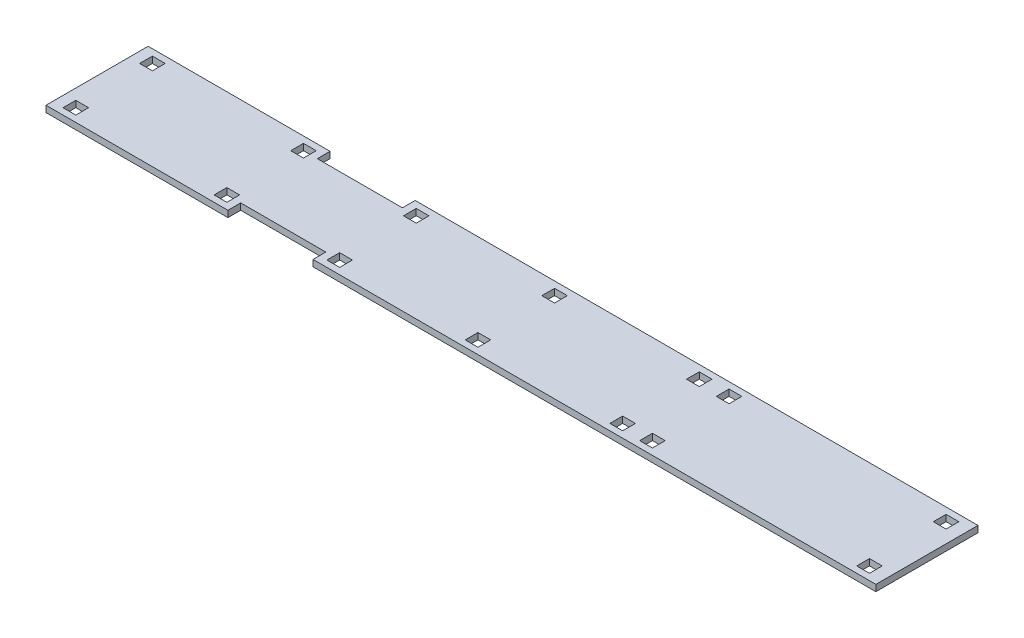
SolidWorks part; units mm, degrees
ref_plane "Front Plane" through (0, 0, 0) normal (0, 0, 1) x (1, 0, 0)
ref_plane "Top Plane" through (0, 0, 0) normal (0, 1, 0) x (1, 0, 0)
ref_plane "Right Plane" through (0, 0, 0) normal (1, 0, 0) x (0, 0, -1)
sketch "Sketch1" plane through (0, 0, 0) normal (0, 1, 0) x (1, 0, 0)
  line L0 (64.5, 4.5) -> (67.5, 4.5)
  line L1 (0, 0) -> (195, 0)
  line L2 (0, 0) -> (0, 24)
  line L3 (0, 24) -> (195, 24)
  line L4 (195, 0) -> (195, 24)
  line L5 (2.5, 22.5) -> (5.5, 22.5)
  line L6 (2.5, 22.5) -> (2.5, 19.5)
  line L7 (2.5, 19.5) -> (5.5, 19.5)
  line L8 (5.5, 22.5) -> (5.5, 19.5)
  line L9 (2.5, 22.5) -> (5.5, 19.5) construction
  line L10 (2.5, 19.5) -> (5.5, 22.5) construction
  line L11 (64.5, 4.5) -> (64.5, 1.5)
  line L12 (64.5, 1.5) -> (67.5, 1.5)
  line L13 (67.5, 4.5) -> (67.5, 1.5)
  line L14 (64.5, 4.5) -> (67.5, 1.5) construction
  line L15 (64.5, 1.5) -> (67.5, 4.5) construction
  line L16 (38, 4.5) -> (41, 4.5)
  line L17 (97, 4.5) -> (100, 4.5)
  line L18 (97, 4.5) -> (97, 1.5)
  line L19 (97, 1.5) -> (100, 1.5)
  line L20 (100, 4.5) -> (100, 1.5)
  line L21 (97, 4.5) -> (100, 1.5) construction
  line L22 (97, 1.5) -> (100, 4.5) construction
  line L23 (38, 4.5) -> (38, 1.5)
  line L24 (38, 1.5) -> (41, 1.5)
  line L25 (41, 4.5) -> (41, 1.5)
  line L26 (38, 4.5) -> (41, 1.5) construction
  line L27 (38, 1.5) -> (41, 4.5) construction
  line L28 (138, 4.5) -> (141, 4.5)
  line L29 (138, 22.5) -> (141, 22.5)
  line L30 (138, 22.5) -> (138, 19.5)
  line L31 (138, 19.5) -> (141, 19.5)
  line L32 (141, 22.5) -> (141, 19.5)
  line L33 (138, 22.5) -> (141, 19.5) construction
  line L34 (138, 19.5) -> (141, 22.5) construction
  line L35 (138, 4.5) -> (138, 1.5)
  line L36 (138, 1.5) -> (141, 1.5)
  line L37 (141, 4.5) -> (141, 1.5)
  line L38 (138, 4.5) -> (141, 1.5) construction
  line L39 (138, 1.5) -> (141, 4.5) construction
  line L40 (131, 4.5) -> (134, 4.5)
  line L41 (131, 22.5) -> (134, 22.5)
  line L42 (131, 22.5) -> (131, 19.5)
  line L43 (131, 19.5) -> (134, 19.5)
  line L44 (134, 22.5) -> (134, 19.5)
  line L45 (131, 22.5) -> (134, 19.5) construction
  line L46 (131, 19.5) -> (134, 22.5) construction
  line L47 (131, 4.5) -> (131, 1.5)
  line L48 (131, 1.5) -> (134, 1.5)
  line L49 (134, 4.5) -> (134, 1.5)
  line L50 (131, 4.5) -> (134, 1.5) construction
  line L51 (131, 1.5) -> (134, 4.5) construction
  line L52 (64.5, 22.5) -> (67.5, 22.5)
  line L53 (97, 22.5) -> (100, 22.5)
  line L54 (97, 22.5) -> (97, 19.5)
  line L55 (97, 19.5) -> (100, 19.5)
  line L56 (100, 22.5) -> (100, 19.5)
  line L57 (97, 22.5) -> (100, 19.5) construction
  line L58 (97, 19.5) -> (100, 22.5) construction
  line L59 (64.5, 22.5) -> (64.5, 19.5)
  line L60 (64.5, 19.5) -> (67.5, 19.5)
  line L61 (67.5, 22.5) -> (67.5, 19.5)
  line L62 (64.5, 22.5) -> (67.5, 19.5) construction
  line L63 (64.5, 19.5) -> (67.5, 22.5) construction
  line L64 (38, 22.5) -> (41, 22.5)
  line L65 (2.5, 4.5) -> (5.5, 4.5)
  line L66 (2.5, 4.5) -> (2.5, 1.5)
  line L67 (2.5, 1.5) -> (5.5, 1.5)
  line L68 (5.5, 4.5) -> (5.5, 1.5)
  line L69 (2.5, 4.5) -> (5.5, 1.5) construction
  line L70 (2.5, 1.5) -> (5.5, 4.5) construction
  line L71 (38, 22.5) -> (38, 19.5)
  line L72 (38, 19.5) -> (41, 19.5)
  line L73 (41, 22.5) -> (41, 19.5)
  line L74 (38, 22.5) -> (41, 19.5) construction
  line L75 (38, 19.5) -> (41, 22.5) construction
  line L76 (189, 22.5) -> (192, 22.5)
  line L77 (189, 4.5) -> (192, 4.5)
  line L78 (189, 4.5) -> (189, 1.5)
  line L79 (189, 1.5) -> (192, 1.5)
  line L80 (192, 4.5) -> (192, 1.5)
  line L81 (189, 4.5) -> (192, 1.5) construction
  line L82 (189, 1.5) -> (192, 4.5) construction
  line L83 (189, 22.5) -> (189, 19.5)
  line L84 (189, 19.5) -> (192, 19.5)
  line L85 (192, 22.5) -> (192, 19.5)
  line L86 (189, 22.5) -> (192, 19.5) construction
  line L87 (189, 19.5) -> (192, 22.5) construction
  point P10 (4, 21)
  point P14 (66, 3)
  point P15 (13.8504, 11.5574)
  point P16 (0, 0)
  point P22 (98.5, 3)
  point P26 (39.5, 3)
  point P32 (139.5, 21)
  point P36 (139.5, 3)
  point P42 (132.5, 21)
  point P46 (132.5, 3)
  point P47 (25.6536, 17.9962)
  point P53 (98.5, 21)
  point P57 (66, 21)
  point P63 (4, 3)
  point P67 (39.5, 21)
  point P73 (190.5, 3)
  point P77 (190.5, 21)
  point P78 (47.2013, 9.4586)
  point P79 (50.0678, 15.2563)
  point P80 (0, 0)
  point P81 (0, 0)
  point P82 (32.4668, 7.9426)
  point P83 (0, 0)
  point P84 (0, 0)
  point P85 (0, 0)
  point P86 (0, 0)
  point P87 (0, 0)
  point P88 (0, 0)
  point P89 (0, 0)
  point P90 (17.6787, 18.4711)
  dimension "D1" = 24
  dimension "D2" = 195
  dimension "D3" = 3
  dimension "D4" = 18
  dimension "D5" = 3
  dimension "D6" = 35.5
  dimension "D7" = 26.5
  dimension "D8" = 32.5
  dimension "D9" = 34
  dimension "D10" = 51
  dimension "D11" = 7
  dimension "D12" = 4
extrude "Boss-Extrude1" add sketch "Sketch1" along normal blind 1.5
sketch "Sketch2" plane through (0, 1.5, 0) normal (0, 1, 0) x (1, 0, 0)
  line L0 (0, 0) -> (195, 0) construction
  line L1 (42.75, 0) -> (62.75, 0)
  line L2 (42.75, 0) -> (42.75, 3)
  line L3 (42.75, 3) -> (62.75, 3)
  line L4 (62.75, 0) -> (62.75, 3)
  line L5 (42.75, 0) -> (62.75, 3) construction
  line L6 (42.75, 3) -> (62.75, 0) construction
  line L7 (41, 4.5) -> (38, 4.5) construction
  line L8 (195, 24) -> (0, 24) construction
  line L9 (42.75, 24) -> (62.75, 24)
  line L10 (42.75, 24) -> (42.75, 21)
  line L11 (42.75, 21) -> (62.75, 21)
  line L12 (62.75, 24) -> (62.75, 21)
  line L13 (42.75, 24) -> (62.75, 21) construction
  line L14 (42.75, 21) -> (62.75, 24) construction
  point P4 (52.75, 1.5)
  point P9 (39.5, 4.5)
  point P16 (52.75, 22.5)
  point P17 (0, 0)
  dimension "D1" = 3
  dimension "D2" = 13.25
  dimension "D3" = 20
extrude "Cut-Extrude1" cut sketch "Sketch2" against normal blind 1.5 contours L1 L4 L3 L2 | L11 L12 L9 L10
